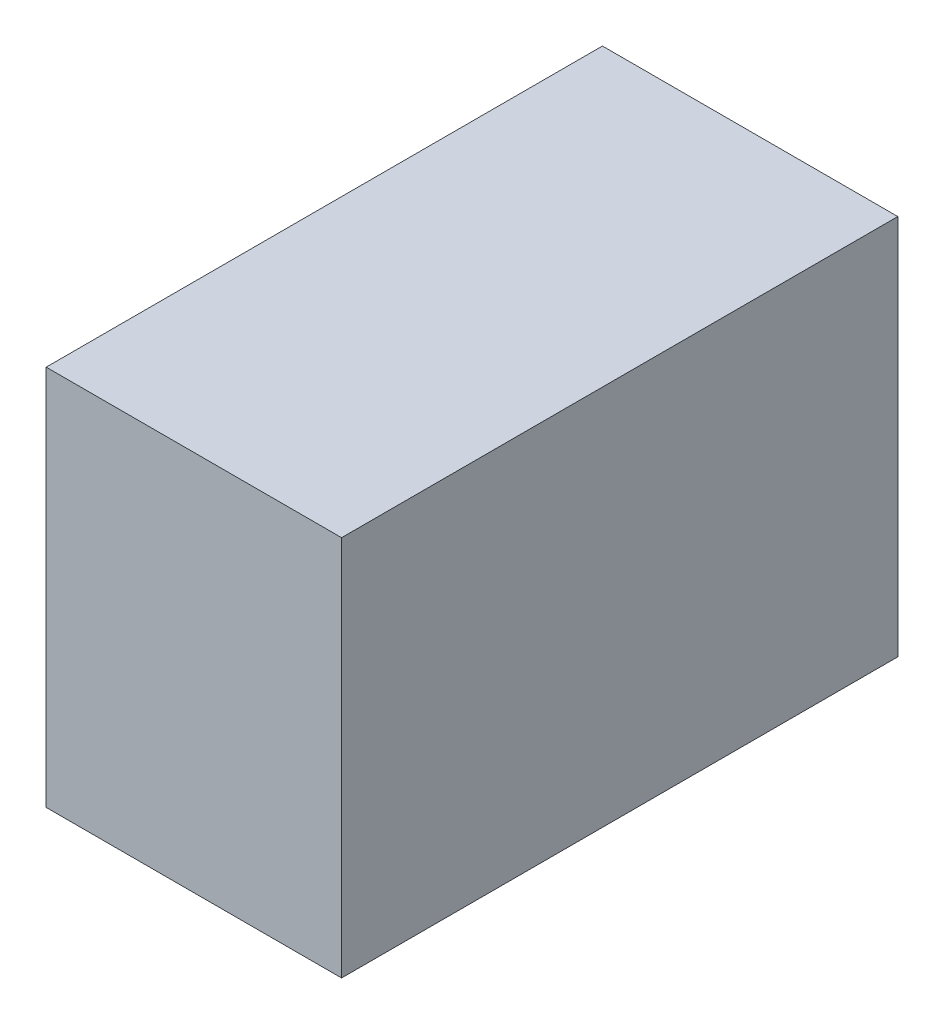
SolidWorks part; units mm, degrees
ref_plane "Front Plane" through (0, 0, 0) normal (0, 0, 1) x (1, 0, 0)
ref_plane "Top Plane" through (0, 0, 0) normal (0, 1, 0) x (1, 0, 0)
ref_plane "Right Plane" through (0, 0, 0) normal (1, 0, 0) x (0, 0, -1)
sketch "Sketch1" plane through (0, 0, 0) normal (0, 0, 1) x (1, 0, 0)
  line L1 (6.22, 53.8411) -> (30, 53.8411)
  line L2 (6.22, 53.8411) -> (6.22, 23.1411)
  line L3 (6.22, 23.1411) -> (30, 23.1411)
  line L4 (30, 53.8411) -> (30, 23.1411)
  dimension "D1" = 30.7
  dimension "D2" = 23.78
extrude "Boss-Extrude1" add sketch "Sketch1" along normal blind 44.78
